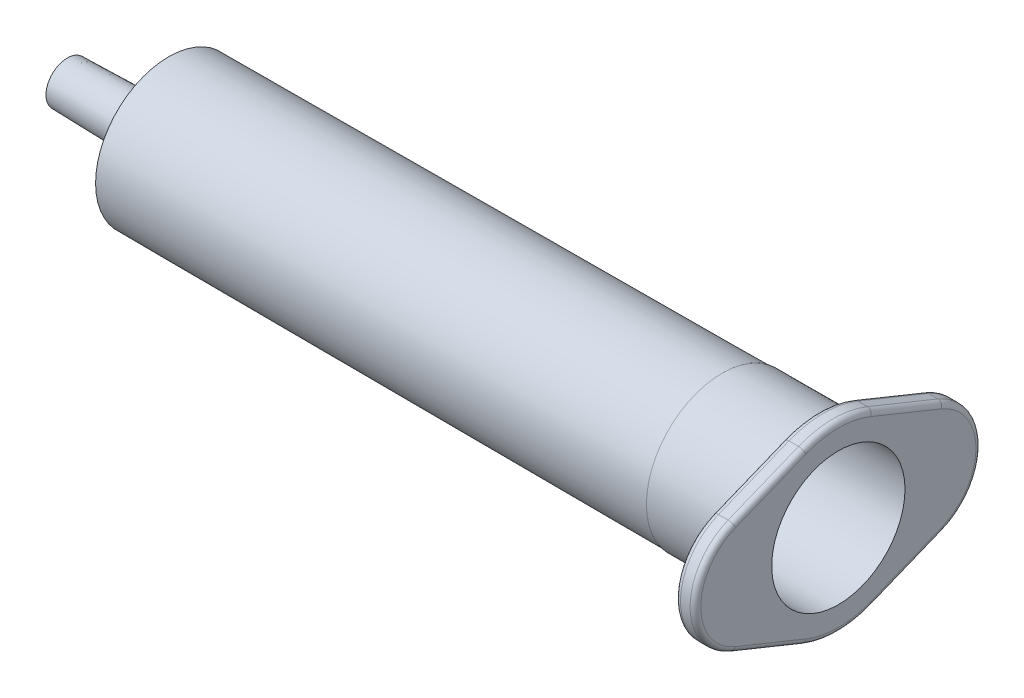
SolidWorks part; units mm, degrees
ref_plane "Front Plane" through (0, 0, 0) normal (0, 0, 1) x (1, 0, 0)
ref_plane "Top Plane" through (0, 0, 0) normal (0, 1, 0) x (1, 0, 0)
ref_plane "Right Plane" through (0, 0, 0) normal (1, 0, 0) x (0, 0, -1)
ref_plane "Plane2" through (72.3, 0, 0) normal (1, 0, 0) x (0, 0, -1)
sketch "Sketch6" plane through (72.3, 0, 0) normal (1, 0, 0) x (0, 0, -1)
  line L0 (-9.8346, -5.2928) -> (0, -9.2799)
  line L1 (0, -9.2799) -> (9.8346, -5.2928)
  line L2 (9.8346, 5.2928) -> (0, 9.2799)
  line L3 (0, 9.2799) -> (-9.8346, 5.2928)
  arc A0 (-9.8346, 5.2928) -> (-9.8346, -5.2928) centre (-7.6888, 0) ccw
  arc A1 (9.8346, -5.2928) -> (9.8346, 5.2928) centre (7.6888, 0) ccw
extrude "Boss-Extrude3" add sketch "Sketch6" against normal blind 1.9 separate body
ref_plane "Plane3" through (0, 0, 0) normal (0, 0, -1) x (-1, 0, 0)
sketch "Sketch11" plane through (0, 0, 0) normal (0, 0, -1) x (-1, 0, 0)
  line L0 (-70.4, 7.1314) -> (-70.4, 0)
  line L1 (-70.4, 0) -> (0, 0)
  line L2 (0, 0) -> (0, 2)
  line L3 (0, 2) -> (-8.5, 2.2)
  line L4 (-8.5, 2.2) -> (-9.5, 6.85)
  line L5 (-9.5, 6.85) -> (-61.4, 7.0312)
  line L6 (-61.4, 7.0312) -> (-61.4, 7.1)
  line L7 (-61.4, 7.1) -> (-70.4, 7.1314)
  line L8 (-70.4, 0) -> (0, 0) construction
revolve "Revolve1" add sketch "Sketch11" angle 360 about L1
hole_wizard "Hole1" positions "Sketch13" profile "Sketch12" legacy
sketch "Sketch13" plane through (72.3, 0, 0) normal (1, 0, 0) x (0, 0, -1)
  point P0 (0, 0)
sketch "Sketch12" plane through (72.3, 0, 0) normal (0, 1, 0) x (0, 0, -1)
  line L0 (0, 0) -> (0, 72.3)
  line L1 (0, 72.3) -> (1, 72.3)
  line L2 (1, 72.3) -> (1, 63.2398)
  line L3 (1, 63.2398) -> (6.25, 62.1107)
  line L4 (6.25, 62.1107) -> (6.25, 0)
  line L5 (6.25, 0) -> (0, 0)
  line L6 (0, -6.13) -> (0, 109.2824) construction
  line L7 (-1, 63.2398) -> (-6.25, 62.1107) construction
  line L8 (0, 72.3) -> (-1, 72.3) construction
  dimension "Diameter" = 2
  dimension "Depth" = 72.3
  dimension "C-Drill Diameter" = 12.5
  dimension "C-Drill Depth" = 62.1107
  dimension "C-Drill Angle" = 155.726
fillet "Fillet4" radius 8.6 2 edges at (71.35, -9.2799, 0) (71.35, 9.2799, 0)
fillet "Fillet5" radius 0.25 1 edges at (9.0602, 0, -1)
fillet "Fillet6" radius 0.5 17 edges at (70.4, 6.6313, 6.5329) (70.4, 0, 13.4) (70.4, 8.6, 0) (70.4, -6.6313, 6.5329) (70.4, 6.6313, -6.5329) (70.4, -8.6, 0) (70.4, 0, -13.4) (70.4, -6.6313, -6.5329) (72.3, 0, -13.4) (72.3, 6.6313, -6.5329) (72.3, -6.6313, -6.5329) (72.3, 8.6, 0) (72.3, -8.6, 0) (72.3, 6.6313, 6.5329) (72.3, -6.6313, 6.5329) (72.3, 0, 13.4) (70.4, 0, 7.1314)
fillet "Fillet7" radius 1 1 edges at (8.5, 0, 2.2)
